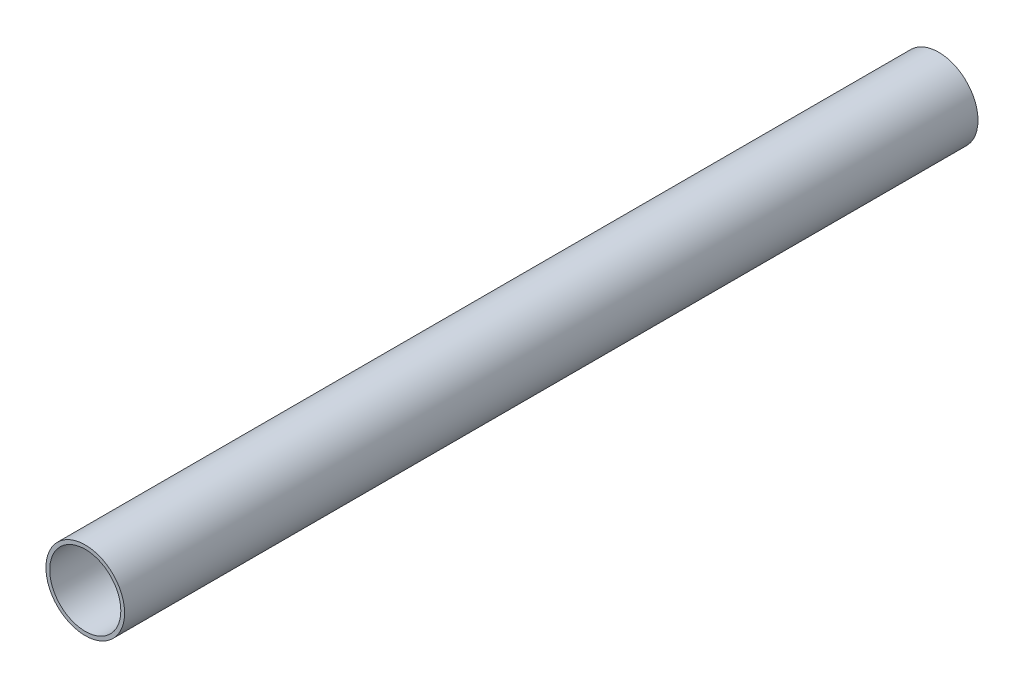
SolidWorks part; units mm, degrees
ref_plane "Front Plane" through (0, 0, 0) normal (0, 0, 1) x (1, 0, 0)
ref_plane "Top Plane" through (0, 0, 0) normal (0, 1, 0) x (1, 0, 0)
ref_plane "Right Plane" through (0, 0, 0) normal (1, 0, 0) x (0, 0, -1)
sketch "Sketch1" plane through (0, 0, 0) normal (0, 0, 1) x (1, 0, 0)
  line L0 (14.0462, 0) -> (12.7, 0) construction
  circle A0 centre (0, 0) radius 14.0462
  dimension "D2" = 1.3462
  dimension "D1" = 28.0924
extrude "Extrude-Thin1" add sketch "Sketch1" along normal mid plane 304.8 thin thin type one direction reverse wall 1.3462
equation "\"D2@Sketch1\" = \"D5@Extrude-Thin1\""
